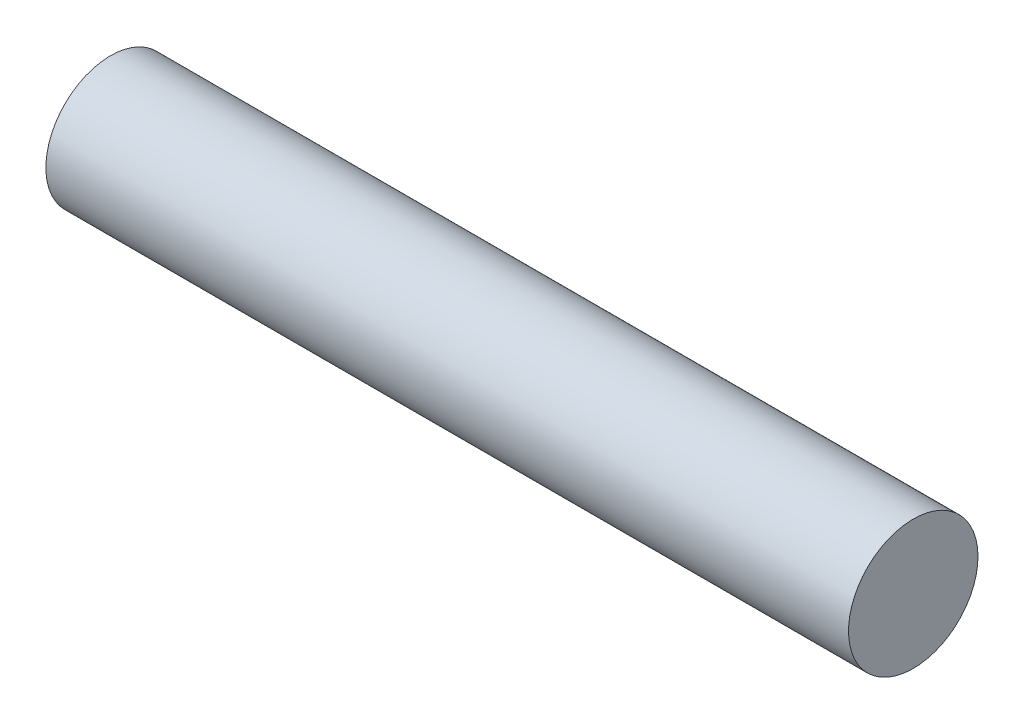
SolidWorks part; units mm, degrees
material "Plain Carbon Steel"
ref_plane "Front Plane" through (0, 0, 0) normal (0, 0, 1) x (1, 0, 0)
ref_plane "Top Plane" through (0, 0, 0) normal (0, 1, 0) x (1, 0, 0)
ref_plane "Right Plane" through (0, 0, 0) normal (1, 0, 0) x (0, 0, -1)
sketch "Sketch1" plane through (0, 0, 0) normal (1, 0, 0) x (0, 0, -1)
  circle A0 centre (0, 0) radius 0.9525
  dimension "D1" = 1.905
extrude "Boss-Extrude1" add sketch "Sketch1" along normal mid plane 11.811 contours A0
